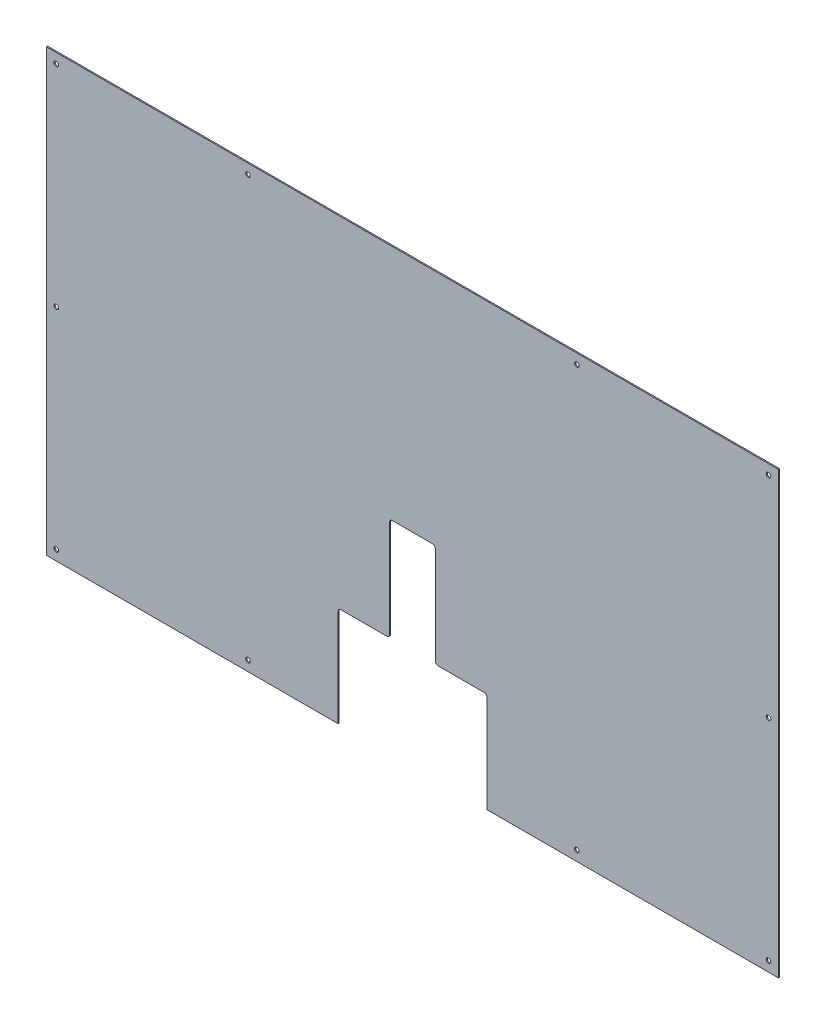
SolidWorks part; units mm, degrees
ref_plane "Front Plane" through (0, 0, 0) normal (0, 0, 1) x (1, 0, 0)
ref_plane "Top Plane" through (0, 0, 0) normal (0, 1, 0) x (1, 0, 0)
ref_plane "Right Plane" through (0, 0, 0) normal (1, 0, 0) x (0, 0, -1)
sketch "Sketch1" plane through (0, 0, 0) normal (0, 0, 1) x (1, 0, 0)
  line L0 (0, 0) -> (0, 770)
  line L1 (0, 770) -> (1280, 770)
  line L2 (1280, 770) -> (1280, 0)
  line L3 (1280, 0) -> (770, 0)
  line L4 (17.5, 1015.765) -> (17.5, -38.2763) construction
  line L5 (515, 175) -> (595, 175)
  line L6 (510, 0) -> (510, 170)
  line L7 (600, 180) -> (600, 350)
  line L8 (680, 180) -> (680, 350)
  line L9 (770, 0) -> (770, 170)
  line L10 (765, 175) -> (685, 175)
  line L11 (605, 355) -> (675, 355)
  line L12 (510, 0) -> (0, 0)
  line L13 (-71.4311, 752.5) -> (1330.837, 752.5) construction
  line L14 (640, 770) -> (640, 117.1152) construction
  line L15 (1262.5, 1015.765) -> (1262.5, -38.2763) construction
  line L16 (0, 385) -> (1345.8145, 385) construction
  line L17 (-71.4311, 17.5) -> (1330.837, 17.5) construction
  circle A0 centre (17.5, 752.5) radius 4
  circle A1 centre (1262.5, 752.5) radius 4
  circle A2 centre (1262.5, 17.5) radius 4
  circle A3 centre (17.5, 17.5) radius 4
  circle A4 centre (352.5, 752.5) radius 4
  circle A5 centre (927.5, 752.5) radius 4
  circle A6 centre (927.5, 17.5) radius 4
  circle A7 centre (352.5, 17.5) radius 4
  circle A8 centre (17.5, 385) radius 4
  circle A9 centre (1262.5, 385) radius 4
  arc A10 (510, 170) -> (515, 175) centre (515, 170) cw
  arc A11 (770, 170) -> (765, 175) centre (765, 170) ccw
  arc A12 (685, 175) -> (680, 180) centre (685, 180) cw
  arc A13 (595, 175) -> (600, 180) centre (595, 180) ccw
  arc A14 (680, 350) -> (675, 355) centre (675, 350) ccw
  arc A15 (605, 355) -> (600, 350) centre (605, 350) ccw
  dimension "D3" = 335
  dimension "D4" = 5
  dimension "D1" = 17.5
  dimension "D2" = 17.5
  dimension "D5" = 770
  dimension "D6" = 1280
  dimension "D7" = 170
  dimension "D8" = 70
  dimension "D9" = 170
extrude "Boss-Extrude1" add sketch "Sketch1" along normal blind 2
